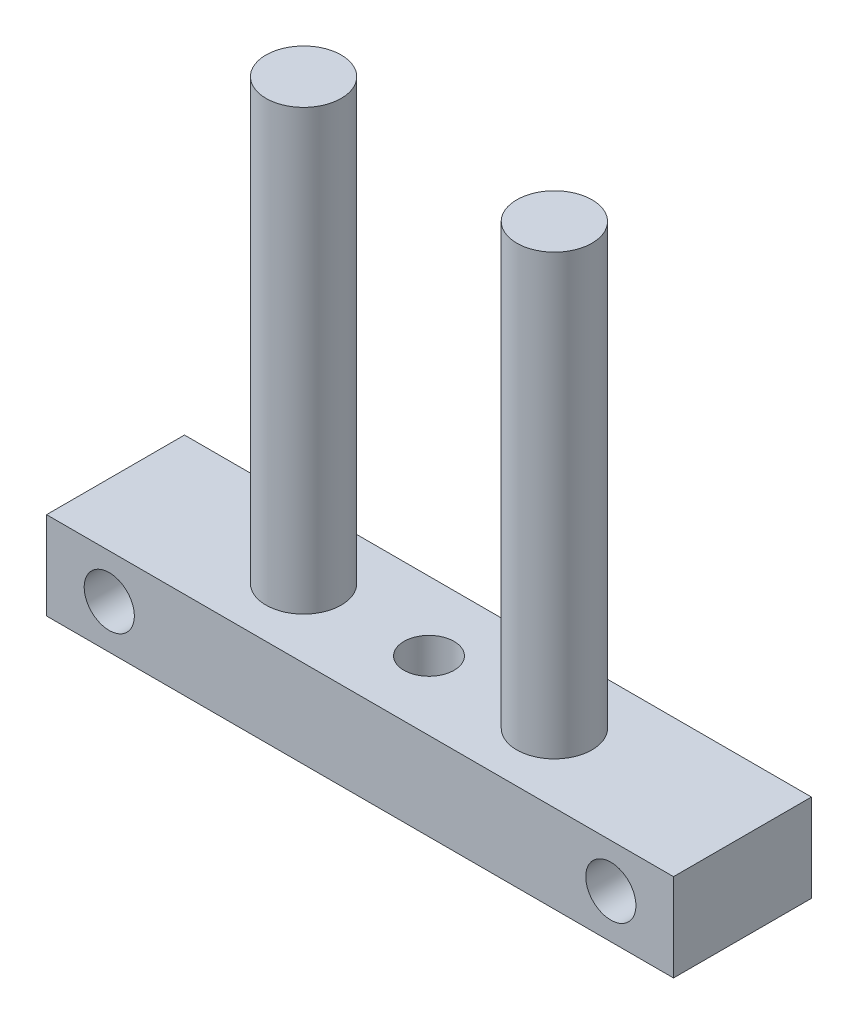
SolidWorks part; units mm, degrees
ref_plane "Front Plane" through (0, 0, 0) normal (0, 0, 1) x (1, 0, 0)
ref_plane "Top Plane" through (0, 0, 0) normal (0, 1, 0) x (1, 0, 0)
ref_plane "Right Plane" through (0, 0, 0) normal (1, 0, 0) x (0, 0, -1)
sketch "Sketch1" plane through (0, 0, 0) normal (0, 0, 1) x (1, 0, 0)
  line L1 (-25, -3.5) -> (25, -3.5)
  line L2 (-25, -3.5) -> (-25, 3.5)
  line L3 (-25, 3.5) -> (25, 3.5)
  line L4 (25, -3.5) -> (25, 3.5)
  line L5 (-25, -3.5) -> (25, 3.5) construction
  line L6 (-25, 3.5) -> (25, -3.5) construction
  point P0 (0, 0)
  dimension "D1" = 7
  dimension "D2" = 50
extrude "Boss-Extrude1" add sketch "Sketch1" along normal blind 11
sketch "Sketch2" plane through (0, 0, 0) normal (0, 0, -1) x (-1, 0, 0)
  circle A6 centre (20, 0) radius 2
  circle A7 centre (-20, 0) radius 2
extrude "Cut-Extrude1" cut sketch "Sketch2" against normal through all
sketch "Sketch3" plane through (0, -3.5, 0) normal (0, -1, 0) x (1, 0, 0)
  circle A2 centre (0, 5.5) radius 2
extrude "Cut-Extrude2" cut sketch "Sketch3" against normal through all
sketch "Sketch4" plane through (0, 3.5, 0) normal (0, 1, 0) x (1, 0, 0)
  circle A2 centre (-10, -5.5) radius 3
  circle A3 centre (10, -5.5) radius 3
extrude "Boss-Extrude2" add sketch "Sketch4" along normal blind 35
